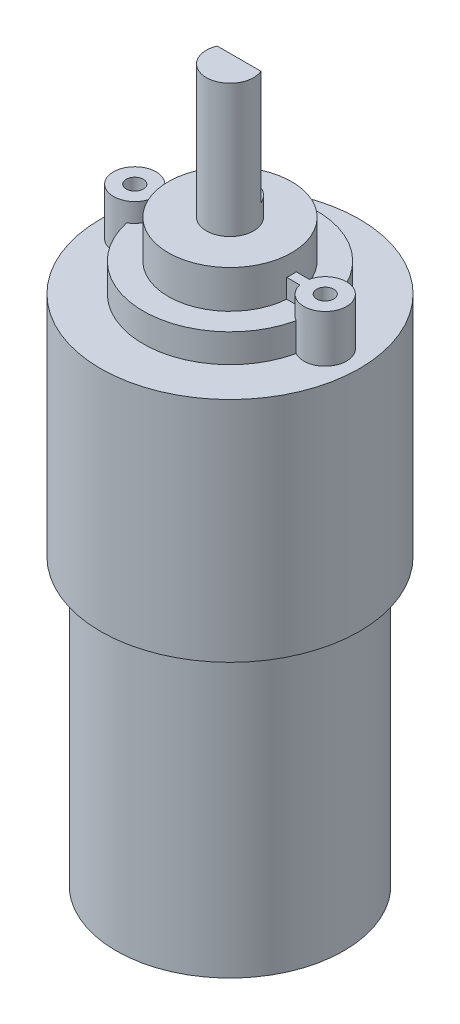
SolidWorks part; units mm, degrees
ref_plane "Alzado" through (0, 0, 0) normal (0, 0, 1) x (1, 0, 0)
ref_plane "Planta" through (0, 0, 0) normal (0, 1, 0) x (1, 0, 0)
ref_plane "Vista lateral" through (0, 0, 0) normal (1, 0, 0) x (0, 0, -1)
sketch "Croquis1" plane through (0, 0, 0) normal (0, 0, 1) x (1, 0, 0)
  line L0 (0, 65.6872) -> (0, -89.1873) construction
  line L1 (0, 30.5) -> (-6.5, 30.5)
  line L2 (-6.5, 30.5) -> (-6.5, 26.5)
  line L3 (-6.5, 26.5) -> (-9.15, 26.5)
  line L4 (-9.15, 26.5) -> (-9.15, 23.5)
  line L5 (-9.15, 23.5) -> (-13.65, 23.5)
  line L6 (-13.65, 23.5) -> (-13.65, -0.5)
  line L7 (-13.65, -0.5) -> (-12, -0.5)
  line L8 (-12, -0.5) -> (-12, -30.5)
  line L9 (-12, -30.5) -> (0, -30.5)
  line L10 (0, -30.5) -> (0, 30.5)
  line L11 (0, 30.5) -> (0, 44.5)
  line L12 (0, 44.5) -> (-2.5, 44.5)
  line L13 (-2.5, 44.5) -> (-2.5, 30.5)
  line L14 (-2.5, 30.5) -> (0, 30.5)
  point P5 (0, 0)
  dimension "D1" = 6.5
  dimension "D2" = 4
  dimension "D3" = 9.15
  dimension "D4" = 13.65
  dimension "D5" = 24
  dimension "D6" = 30
  dimension "D7" = 3
  dimension "D8" = 12
  dimension "D9" = 14
  dimension "D10" = 2.5
revolve "Revolución1" add sketch "Croquis1" angle 360 about L0
sketch "Croquis2" plane through (0, 44.5, 0) normal (0, 1, 0) x (1, 0, 0)
  line L0 (-2.3083, 0.96) -> (2.3083, 0.96)
  circle A1 centre (0, 0) radius 2.5
  circle A2 centre (0, 0) radius 2.5
  circle M3 centre (0, 0) radius 2.5
  dimension "D2" = 0.96
  dimension "D1" = 0
extrude "Cortar-Extruir1" cut sketch "Croquis2" against normal blind 12 contours L0 M3
sketch "Croquis4" plane through (0, 23.5, 0) normal (0, 1, 0) x (1, 0, 0)
  line L0 (0, 5.4331) -> (0, -4.2682) construction
  line L1 (9, 0.5) -> (-9, 0.5)
  line L2 (0, 0.5) -> (0, -0.5)
  line L3 (9, -0.5) -> (-9, -0.5)
  line L4 (-9, 0.5) -> (-9, -0.5)
  line L5 (-12.29, 7.8034) -> (-12.29, -7.8344) construction
  line L6 (0, 0) -> (-16.243, 0) construction
  line L7 (9, 0.5) -> (9, -0.5)
  circle A0 centre (-10.04, 0) radius 2.25
  circle A1 centre (-10.04, 0) radius 0.9
  circle A2 centre (10.04, 0) radius 0.9
  circle A3 centre (10.04, 0) radius 2.25
  point P10 (0, 0)
  point P15 (0, 0)
  circle M11 centre (0, 0) radius 9.15
  dimension "D1" = 1.8
  dimension "D2" = 4.5
  dimension "D3" = 1
  dimension "D4" = 12.29
  dimension "D5" = 9
extrude "Saliente-Extruir1" add sketch "Croquis4" along normal blind 5 contours A1 A0 M11 | A1 A0 L3 L4 L1 M11 | A0 L3 L2 L1 | L3 A3 L1 L2 | A3 A2 L1 L7 L3 M11 | A3 L3 L7 L1 | A3 A2 M11 | L3 A0 L1 L4
